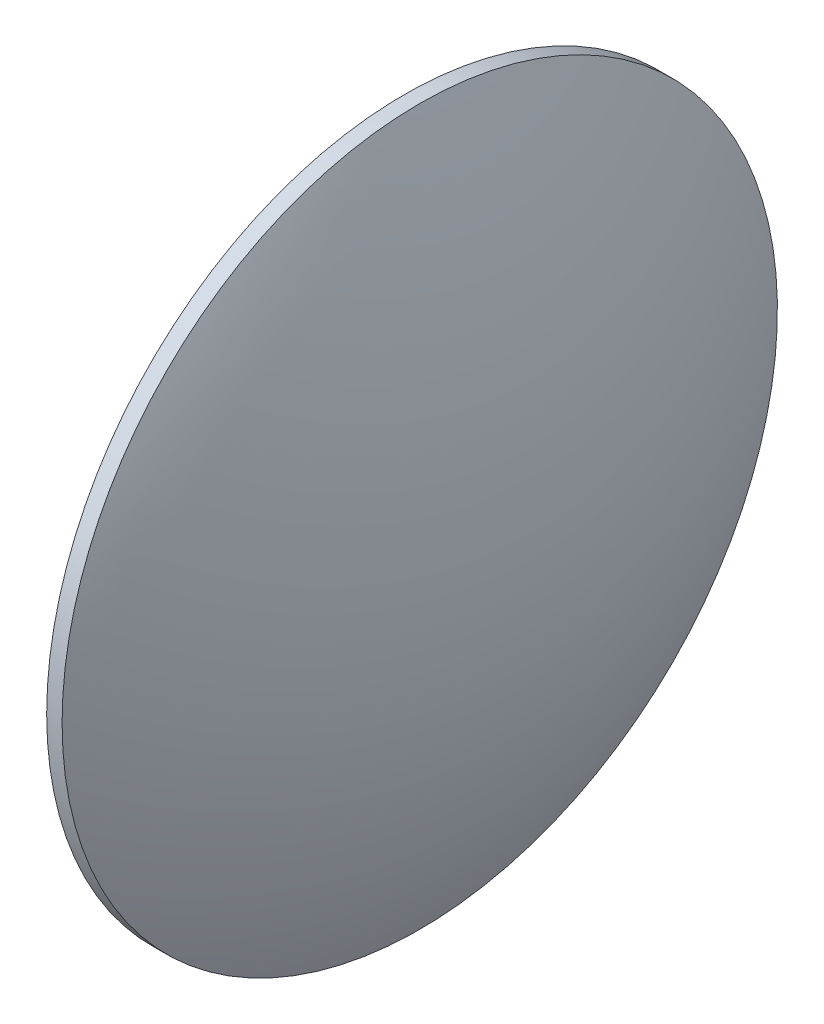
SolidWorks part; units mm, degrees
ref_plane "前视基准面" through (0, 0, 0) normal (0, 0, 1) x (1, 0, 0)
ref_plane "上视基准面" through (0, 0, 0) normal (0, 1, 0) x (1, 0, 0)
ref_plane "右视基准面" through (0, 0, 0) normal (1, 0, 0) x (0, 0, -1)
sketch "草图1" plane through (0, 0, 0) normal (0, 0, 1) x (1, 0, 0)
  line L0 (543.8709, 55.908) -> (563.0471, 55.908) construction
  line L1 (548.5191, 55.908) -> (548.5191, 78.408)
  line L2 (548.5191, 78.408) -> (549.4891, 78.408)
  line L3 (554.6191, 55.908) -> (548.5191, 55.908)
  arc A0 (554.6191, 55.908) -> (549.4891, 78.408) centre (502.712, 55.908) ccw
revolve "旋转1" add sketch "草图1" angle 360 about L0
